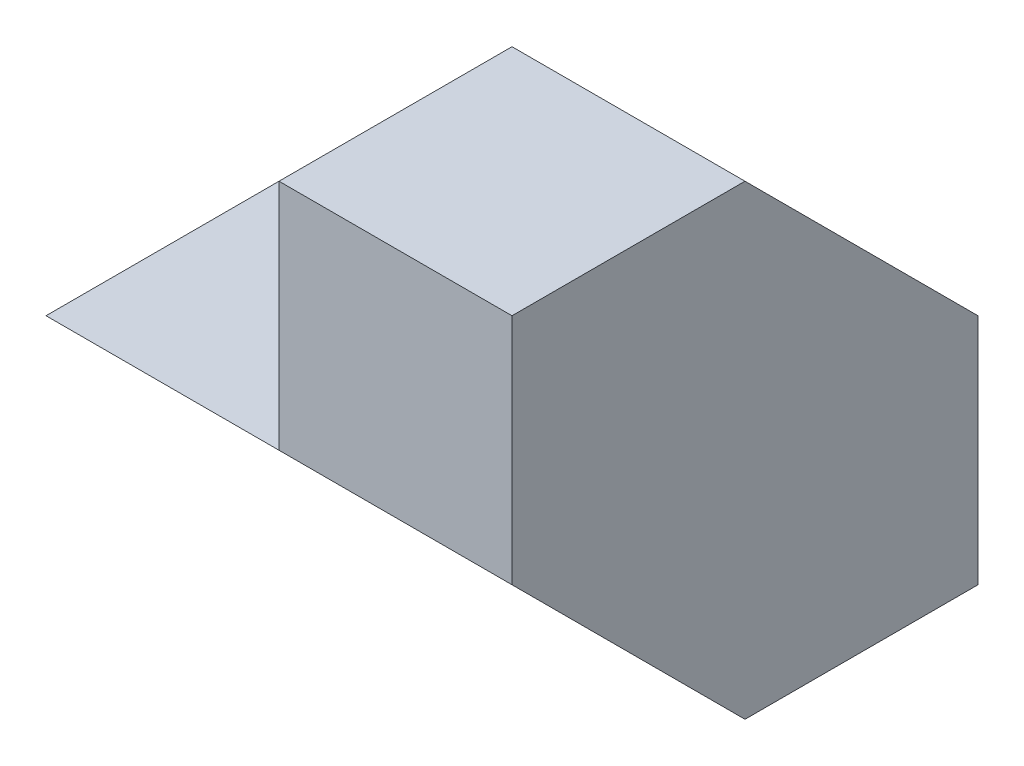
SolidWorks part; units mm, degrees
ref_plane "Front Plane" through (0, 0, 0) normal (0, 0, 1) x (1, 0, 0)
ref_plane "Top Plane" through (0, 0, 0) normal (0, 1, 0) x (1, 0, 0)
ref_plane "Right Plane" through (0, 0, 0) normal (1, 0, 0) x (0, 0, -1)
sketch "Sketch1" plane through (0, 0, 0) normal (0, 0, 1) x (1, 0, 0)
  line L1 (0, 0) -> (40, 0)
  line L2 (0, 0) -> (0, 20)
  line L3 (0, 20) -> (40, 20)
  line L4 (40, 0) -> (40, 20)
  dimension "D1" = 40
  dimension "D2" = 20
extrude "Boss-Extrude1" add sketch "Sketch1" along normal blind 40
sketch "Sketch2" plane through (0, 0, 0) normal (-1, 0, 0) x (0, 0, 1)
  line L0 (40, 20) -> (20, 0)
  line L1 (40, 0) -> (0, 0) construction
  line L2 (20, 0) -> (40, 0)
  line L3 (40, 0) -> (40, 20)
extrude "Cut-Extrude1" cut sketch "Sketch2" against normal blind 40
sketch "Sketch4" plane through (0, 0, 0) normal (0, 0, -1) x (-1, 0, 0)
  line L1 (-40, 20) -> (-20, 20)
  line L2 (-40, 20) -> (-40, 40)
  line L3 (-40, 40) -> (-20, 40)
  line L4 (-20, 20) -> (-20, 40)
  dimension "D1" = 20
  dimension "D2" = 20
extrude "Boss-Extrude3" add sketch "Sketch4" against normal blind 40
sketch "Sketch5" plane through (20, 0, 0) normal (-1, 0, 0) x (0, 0, 1)
  line L0 (0, 20) -> (20, 40)
  line L1 (40, 40) -> (0, 40) construction
  line L2 (20, 40) -> (0, 40)
  line L3 (0, 40) -> (0, 20)
extrude "Cut-Extrude2" cut sketch "Sketch5" against normal blind 40
